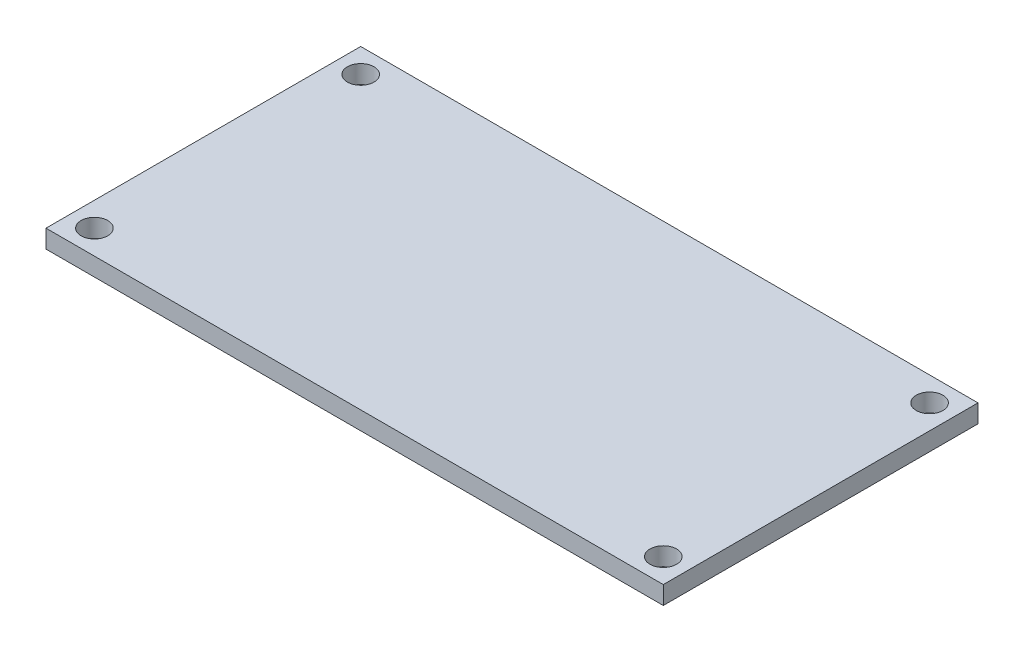
SolidWorks part; units mm, degrees
ref_plane "Спереди" through (0, 0, 0) normal (0, 0, 1) x (1, 0, 0)
ref_plane "Сверху" through (0, 0, 0) normal (0, 1, 0) x (1, 0, 0)
ref_plane "Справа" through (0, 0, 0) normal (1, 0, 0) x (0, 0, -1)
sketch "Эскиз1" plane through (0, 0, 0) normal (0, 1, 0) x (1, 0, 0)
  line L1 (0, 0) -> (51, 0)
  line L2 (0, 0) -> (0, 26)
  line L3 (0, 26) -> (51, 26)
  line L4 (51, 0) -> (51, 26)
  circle A0 centre (2, 2) radius 1.1
  circle A1 centre (49, 2) radius 1.1
  circle A2 centre (49, 24) radius 1.1
  circle A3 centre (2, 24) radius 1.1
  dimension "D1" = 51
  dimension "D2" = 26
  dimension "D3" = 2
  dimension "D4" = 2
  dimension "D5" = 2
  dimension "D6" = 2
extrude "Бобышка-Вытянуть1" add sketch "Эскиз1" along normal blind 1.5
